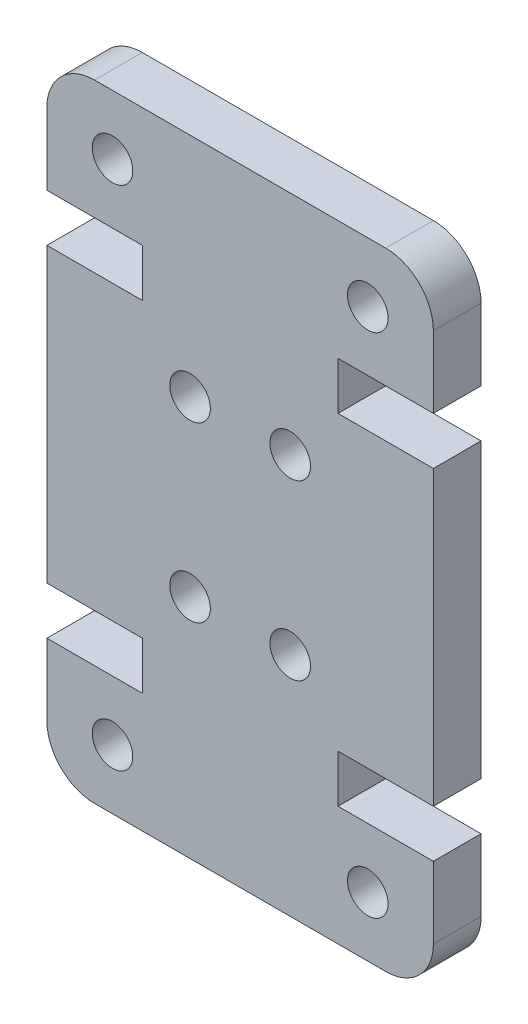
SolidWorks part; units mm, degrees
ref_plane "Front Plane" through (0, 0, 0) normal (0, 0, 1) x (1, 0, 0)
ref_plane "Top Plane" through (0, 0, 0) normal (0, 1, 0) x (1, 0, 0)
ref_plane "Right Plane" through (0, 0, 0) normal (1, 0, 0) x (0, 0, -1)
sketch "Sketch2" plane through (0, 0, 0) normal (0, 0, 1) x (1, 0, 0)
  line L0 (0, 13.13) -> (16.2, 13.13) construction
  line L1 (8.1, 26.26) -> (8.1, 0) construction
  line L2 (0, 7) -> (0, 19.26)
  line L3 (2, 0) -> (14.2, 0)
  line L4 (16.2, 2) -> (16.2, 5)
  line L5 (12.2, 5) -> (16.2, 5)
  line L6 (16.2, 7) -> (12.2, 7)
  line L7 (12.2, 7) -> (12.2, 5)
  line L8 (16.2, 7) -> (16.2, 19.26)
  line L9 (0, 24.26) -> (0, 21.26)
  line L10 (4, 21.26) -> (0, 21.26)
  line L11 (0, 19.26) -> (4, 19.26)
  line L12 (4, 19.26) -> (4, 21.26)
  line L13 (12.2, 19.26) -> (12.2, 21.26)
  line L14 (16.2, 19.26) -> (12.2, 19.26)
  line L15 (12.2, 21.26) -> (16.2, 21.26)
  line L16 (16.2, 24.26) -> (16.2, 21.26)
  line L17 (2, 26.26) -> (14.2, 26.26)
  line L27 (4, 7) -> (4, 5)
  line L30 (0, 7) -> (4, 7)
  line L32 (4, 5) -> (0, 5)
  line L36 (0, 2) -> (0, 5)
  circle A0 centre (13.45, 2.5) radius 0.85
  circle A1 centre (10.2, 9.5) radius 0.85
  arc A2 (16.2, 2) -> (14.2, 0) centre (14.2, 2) cw
  circle A3 centre (2.75, 23.76) radius 0.85
  circle A4 centre (6, 16.76) radius 0.85
  arc A5 (0, 24.26) -> (2, 26.26) centre (2, 24.26) cw
  arc A6 (16.2, 24.26) -> (14.2, 26.26) centre (14.2, 24.26) ccw
  circle A7 centre (10.2, 16.76) radius 0.85
  circle A8 centre (13.45, 23.76) radius 0.85
  arc A17 (0, 2) -> (2, 0) centre (2, 2) ccw
  circle A19 centre (6, 9.5) radius 0.85
  circle A21 centre (2.75, 2.5) radius 0.85
  point P16 (8.1, 13.13)
  dimension "D1" = 1.7
  dimension "D2" = 2
  dimension "D3" = 2.75
  dimension "D4" = 6
  dimension "D5" = 8.1
  dimension "D6" = 2.5
  dimension "D7" = 5
  dimension "D9" = 9.5
  dimension "D10" = 13.13
extrude "Boss-Extrude1" add sketch "Sketch2" along normal blind 4
sketch "Sketch3" plane through (0, 0, 4) normal (0, 0, 1) x (1, 0, 0)
  line L0 (0, 0) -> (0, 26.26)
  line L1 (0, 26.26) -> (16.2, 26.26)
  line L2 (16.2, 26.26) -> (16.2, 0)
  line L3 (16.2, 0) -> (0, 0)
extrude "Cut-Extrude1" cut sketch "Sketch3" against normal blind 2
equation "\"D5@Sketch2\"= \"fingerWidth@parametersSketch@prostheticParameters.SLDPRT\" / 2'Finger Width"
equation "\"D10@Sketch2\"= ( ( \"HL@parametersSketch@prostheticParameters.SLDPRT\" * 0.196 ) - 4 - 6 ) / 2 'PIP Length"
equation "\"D1@Sketch2\"= 1.5 + \"tol1@parametersSketch@prostheticParameters.SLDPRT\""
